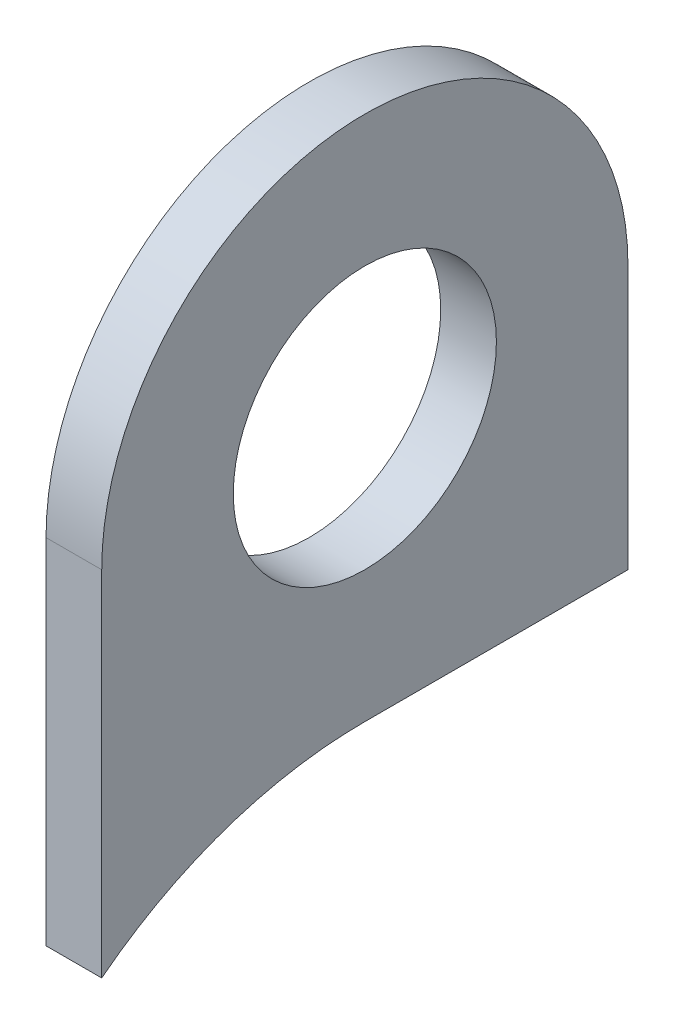
SolidWorks part; units mm, degrees
material "AISI 304"
ref_plane "Front Plane" through (0, 0, 0) normal (0, 0, 1) x (1, 0, 0)
ref_plane "Top Plane" through (0, 0, 0) normal (0, 1, 0) x (1, 0, 0)
ref_plane "Right Plane" through (0, 0, 0) normal (1, 0, 0) x (0, 0, -1)
sketch "Sketch1" plane through (0, 0, 0) normal (1, 0, 0) x (0, 0, -1)
  line L0 (0, 0) -> (0, 60) construction
  line L1 (0, 0) -> (60, 0) construction
  line L2 (60, 0) -> (60, 60)
  line L3 (-60, 0) -> (-60, 60)
  line L4 (-60, 0) -> (-60, -20.621)
  line L5 (0, 0) -> (60, 0)
  circle A0 centre (0, 60) radius 30
  arc A1 (60, 60) -> (-60, 60) centre (0, 60) ccw
  arc A2 (0, 0) -> (-60, -20.621) centre (0, -97.6) ccw
  dimension "D3" = 60
  dimension "D4" = 60
  dimension "D5" = 97.6
  dimension "D1" = 60
  dimension "D2" = 60
extrude "Boss-Extrude1" add sketch "Sketch1" along normal mid plane 12.7
